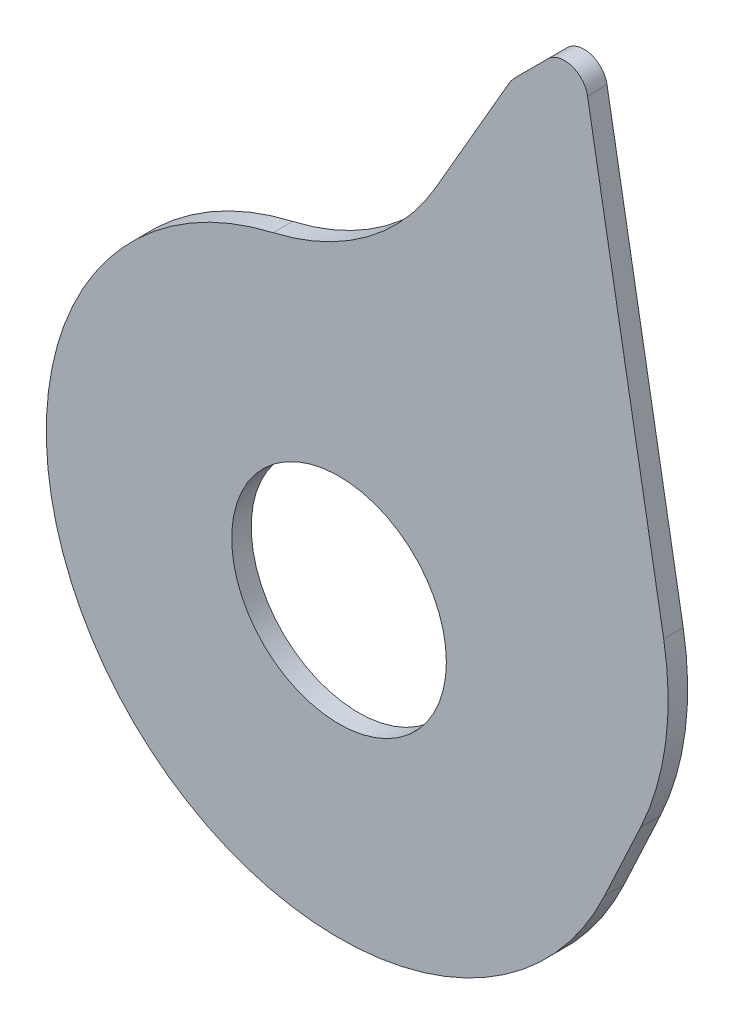
SolidWorks part; units mm, degrees
ref_plane "Plane1" through (0, 0, 0) normal (0, 0, 1) x (1, 0, 0)
ref_plane "Plane2" through (0, 0, 0) normal (0, 1, 0) x (1, 0, 0)
ref_plane "Plane3" through (0, 0, 0) normal (1, 0, 0) x (0, 0, -1)
sketch "Sketch1" plane through (0, 0, 0) normal (0, 0, 1) x (1, 0, 0)
  line L0 (24.7716, 103.9056) -> (43.5164, 136.3726)
  line L1 (45.1056, 138.4437) -> (53.5119, 146.85)
  line L2 (63.6634, 143.6492) -> (83.1743, 32.997)
  line L3 (77.2868, -11.723) -> (67.9731, -31.6964)
  line L4 (0, 0) -> (0, 57.9362) construction
  line L5 (0, 0) -> (38.818, 0) construction
  circle A0 centre (0, 0) radius 27.5
  arc A1 (-16.8858, 73.0744) -> (67.9731, -31.6964) centre (0, 0) ccw
  arc A2 (53.5119, 146.85) -> (63.6634, 143.6492) centre (57.7545, 142.6073) cw
  arc A3 (24.7716, 103.9056) -> (-16.8858, 73.0744) centre (-31.5201, 136.4056) cw
  arc A4 (83.1743, 32.997) -> (77.2868, -11.723) centre (9.3137, 19.9734) cw
  arc A5 (43.5164, 136.3726) -> (45.1056, 138.4437) centre (52.1767, 131.3726) cw
  point P13 (61.6619, 155)
  dimension "D2" = 75
  dimension "D10" = 6
  dimension "D11" = 65
  dimension "D12" = 75
  dimension "D13" = 10
  dimension "D14" = 55
  dimension "D3" = 65
  dimension "D4" = 30
  dimension "D5" = 15
  dimension "D6" = 30.5
  dimension "D7" = 66
  dimension "D8" = 35
  dimension "D9" = 155
extrude "Extrude1" add sketch "Sketch1" along normal blind 5
